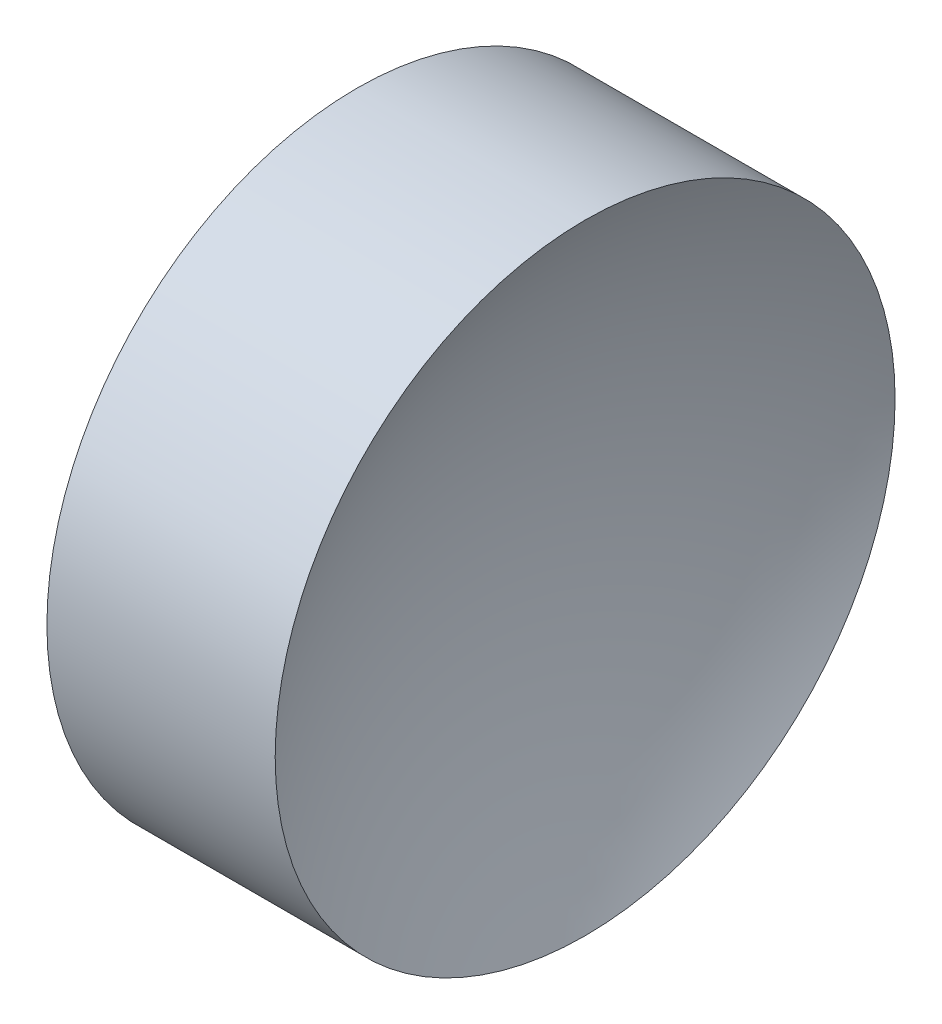
SolidWorks part; units mm, degrees
ref_plane "前视基准面" through (0, 0, 0) normal (0, 0, 1) x (1, 0, 0)
ref_plane "上视基准面" through (0, 0, 0) normal (0, 1, 0) x (1, 0, 0)
ref_plane "右视基准面" through (0, 0, 0) normal (1, 0, 0) x (0, 0, -1)
sketch "草图1" plane through (0, 0, 0) normal (0, 0, 1) x (1, 0, 0)
  line L0 (21.2249, 13.0445) -> (26.692, 13.0445) construction
  line L1 (22.1722, 13.0445) -> (22.1722, 16.1945)
  line L2 (23.672, 13.0445) -> (22.1722, 13.0445)
  line L3 (22.1722, 16.1945) -> (24.4922, 16.1945)
  arc A0 (24.4922, 16.1945) -> (23.672, 13.0445) centre (30.1309, 13.0445) ccw
revolve "旋转1" add sketch "草图1" angle 360 about L0
